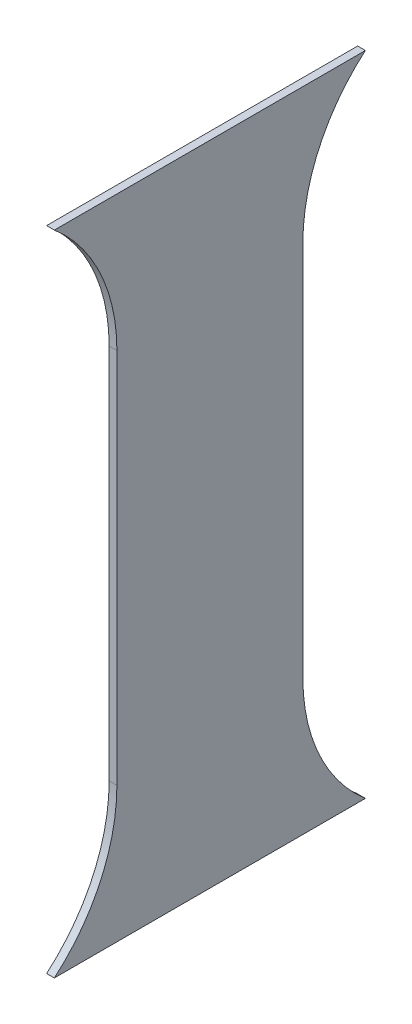
SolidWorks part; units mm, degrees
ref_plane "Front Plane" through (0, 0, 0) normal (0, 0, 1) x (1, 0, 0)
ref_plane "Top Plane" through (0, 0, 0) normal (0, 1, 0) x (1, 0, 0)
ref_plane "Right Plane" through (0, 0, 0) normal (1, 0, 0) x (0, 0, -1)
sketch "Sketch1" plane through (0, 0, 0) normal (1, 0, 0) x (0, 0, -1)
  line L0 (0, 0) -> (0, 972)
  line L1 (-460, -460) -> (940, -460)
  line L3 (940, 1432) -> (-460, 1432)
  line L4 (480, 0) -> (480, 972)
  arc A0 (0, 972) -> (-460, 1432) centre (-460, 972) ccw
  arc A1 (0, 0) -> (-460, -460) centre (-460, 0) cw
  arc A2 (480, 0) -> (940, -460) centre (940, 0) ccw
  arc A3 (480, 972) -> (940, 1432) centre (940, 972) cw
  dimension "D1" = 972
extrude "Boss-Extrude1" add sketch "Sketch1" along normal blind 20
sketch "Sketch2" plane through (20, 0, 0) normal (1, 0, 0) x (0, 0, -1)
  line L1 (-460, 1322) -> (1004.696, 1322)
  line L2 (1004.696, 1322) -> (1004.696, 1530.2277)
  line L3 (1004.696, 1530.2277) -> (-489.3529, 1530.2277)
  line L4 (-489.3529, 1530.2277) -> (-460, 1322)
  line L8 (1004.696, -350) -> (1004.696, -558.2277)
  line L9 (1004.696, -558.2277) -> (-489.3529, -558.2277)
  line L10 (-489.3529, -558.2277) -> (-460, -350)
  line L11 (-460, -350) -> (1004.696, -350)
extrude "Cut-Extrude1" cut sketch "Sketch2" against normal blind 20
